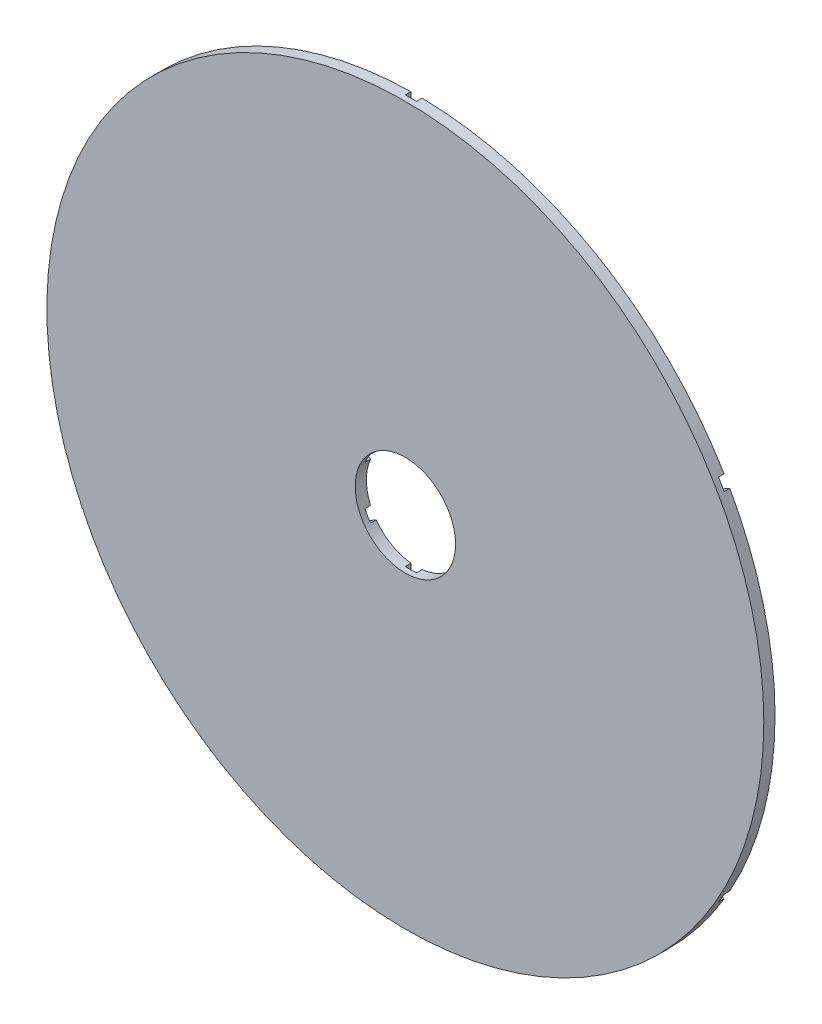
SolidWorks part; units mm, degrees
ref_plane "Front Plane" through (0, 0, 0) normal (0, 0, 1) x (1, 0, 0)
ref_plane "Top Plane" through (0, 0, 0) normal (0, 1, 0) x (1, 0, 0)
ref_plane "Right Plane" through (0, 0, 0) normal (1, 0, 0) x (0, 0, -1)
sketch "Sketch1" plane through (0, 0, 0) normal (0, 0, 1) x (1, 0, 0)
  circle A0 centre (0, 0) radius 101.6
  dimension "D1" = 203.2
extrude "Boss-Extrude1" add sketch "Sketch1" along normal blind 3.175
sketch "Sketch2" plane through (0, 0, 0) normal (0, 0, -1) x (-1, 0, 0)
  line L0 (0, -101.6) -> (0, 101.6) construction
  line L1 (-101.6, 0) -> (101.6, 0) construction
  line L2 (0, 101.6) -> (-87.9882, -50.8) construction
  line L3 (-87.9882, -50.8) -> (87.9882, -50.8) construction
  line L4 (87.9882, -50.8) -> (0, 101.6) construction
  line L5 (-87.9882, -50.8) -> (87.9882, 50.8) construction
  line L6 (87.9882, -50.8) -> (-87.9882, 50.8) construction
  line L7 (-87.1944, -52.1748) -> (88.7819, 49.4252)
  line L8 (88.7819, -49.4252) -> (-87.1944, 52.1748)
  line L9 (1.5875, -101.6) -> (1.5875, 101.6)
  line L10 (-88.7819, -49.4252) -> (87.1944, 52.1748)
  line L11 (87.1944, -52.1748) -> (-88.7819, 49.4252)
  line L12 (-1.5875, -101.6) -> (-1.5875, 101.6)
  circle A0 centre (0, 0) radius 101.6 construction
  circle A2 centre (0, 0) radius 101.6
  circle A3 centre (0, 0) radius 101.6
  point P6 (0, 0)
  point P11 (0, 0)
  circle M9 centre (0, 0) radius 101.6
  dimension "D1" = 30
  dimension "D2" = 1.5875
  dimension "D3" = 1.5875
  dimension "D4" = 0
extrude "Cut-Extrude3" cut sketch "Sketch2" against normal blind 1.5875 contours L7 L12 L11 L10 M9 | L12 L7 L11 | L12 L11 L7 L9 L8 L10 | L11 L9 L7 | L11 L12 L10 | L12 L10 L8 | L10 L8 L9 | L9 L7 L8 | L10 L9 L8 L7 M9 | L11 L8 L7 L9 M9 | L12 L8 L10 L9 M9 | L10 L12 L8 L11 M9 | L12 L9 L11 L7 M9
sketch "Sketch3" plane through (0, 0, 3.175) normal (0, 0, 1) x (1, 0, 0)
  circle A0 centre (0, 0) radius 14.224
  dimension "D1" = 28.448
extrude "Cut-Extrude4" cut sketch "Sketch3" against normal through all
